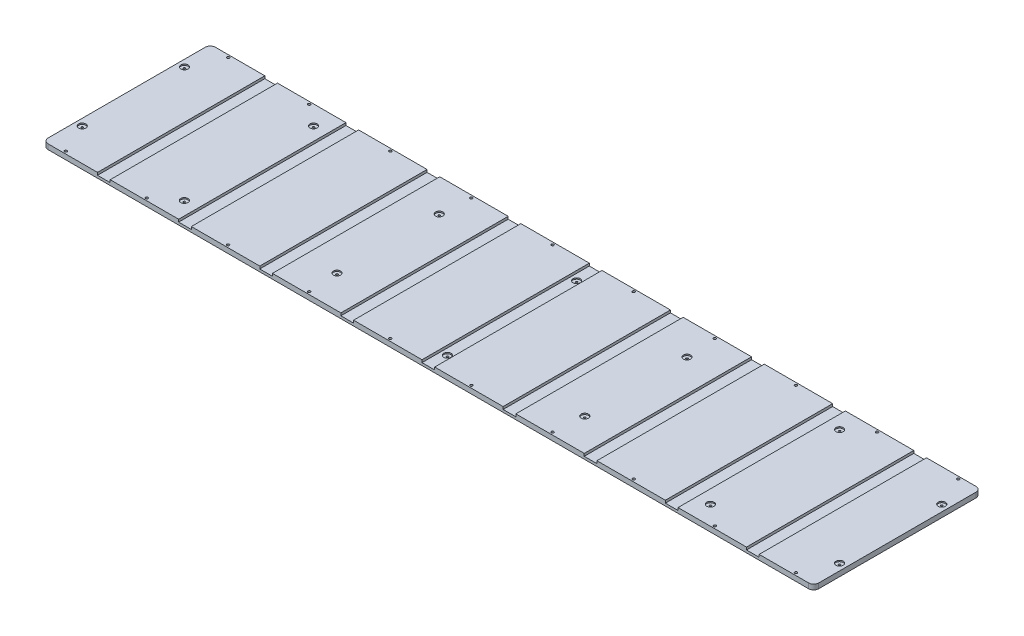
SolidWorks part; units mm, degrees
material "PE High Density"
ref_plane "Front Plane" through (0, 0, 0) normal (0, 0, 1) x (1, 0, 0)
ref_plane "Top Plane" through (0, 0, 0) normal (0, 1, 0) x (1, 0, 0)
ref_plane "Right Plane" through (0, 0, 0) normal (1, 0, 0) x (0, 0, -1)
sketch "Sketch1" plane through (0, 0, 0) normal (0, 1, 0) x (1, 0, 0)
  line L1 (0, 0) -> (1930.4, 0)
  line L2 (0, 0) -> (0, 419.1)
  line L3 (0, 419.1) -> (1930.4, 419.1)
  line L4 (1930.4, 0) -> (1930.4, 419.1)
  dimension "D1" = 1930.4
  dimension "D2" = 419.1
extrude "Boss-Extrude1" add sketch "Sketch1" along normal blind 12.7
sketch "Sketch2" plane through (0, 12.7, 0) normal (0, 1, 0) x (1, 0, 0)
  line L0 (1930.4, 419.1) -> (0, 419.1) construction
  line L2 (0, 419.1) -> (0, 0) construction
  line L3 (965.2, 419.1) -> (965.2, 0) construction
  line L4 (0, 0) -> (1930.4, 0) construction
  circle A0 centre (16.6688, 337.566) radius 2.4511
  circle A1 centre (654.8438, 337.566) radius 2.4511
  circle A2 centre (654.8438, 81.534) radius 2.4511
  circle A3 centre (16.6688, 81.534) radius 2.4511
  circle A4 centre (1275.5562, 337.566) radius 2.4511
  circle A5 centre (1275.5563, 81.534) radius 2.4511
  circle A6 centre (1913.7312, 337.566) radius 2.4511
  circle A7 centre (1913.7312, 81.534) radius 2.4511
  point P0 (16.6688, 337.566)
  point P5 (654.8438, 337.566)
  point P10 (654.8438, 81.534)
  point P17 (16.6688, 81.534)
  point P20 (1293.0187, 337.566)
  point P21 (1293.0187, 81.534)
  point P22 (1931.1937, 81.534)
  point P23 (1931.1937, 337.566)
  point P24 (1275.5562, 337.566)
  point P25 (1275.5563, 81.534)
  point P26 (1913.7312, 81.534)
  point P27 (1913.7312, 337.566)
  point P44 (0, 209.55)
  dimension "D7" = 4.9022
  dimension "D5" = 16.6687
  dimension "D6" = 256.032
  dimension "D4" = 638.175
  dimension "D1" = 128.016
  dimension "D2" = 4
  dimension "D3" = 2
sketch "Sketch7" plane through (0, 12.7, 0) normal (0, 1, 0) x (1, 0, 0)
  line L0 (0, 419.1) -> (0, 0) construction
  line L1 (0, 371.348) -> (1930.4, 371.348) construction
  line L2 (1930.4, 0) -> (1930.4, 419.1) construction
  circle A0 centre (306.324, 371.348) radius 2.4511
  circle A1 centre (306.324, 47.752) radius 2.4511
  circle A2 centre (965.2, 47.752) radius 2.4511
  circle A3 centre (965.2, 371.348) radius 2.4511
  circle A4 centre (1624.076, 371.348) radius 2.4511
  circle A5 centre (1624.076, 47.752) radius 2.4511
  point P0 (306.324, 371.348)
  point P3 (0, 209.55)
  point P8 (965.2, 371.348)
  point P9 (1624.076, 371.348)
  point P13 (965.2, 47.752)
  point P14 (1624.076, 47.752)
  point P18 (306.324, 47.752)
  dimension "D7" = 4.9022
  dimension "D5" = 658.876
  dimension "D6" = 323.596
  dimension "D2" = 161.798
  dimension "D3" = 3
  dimension "D4" = 2
fillet "Fillet1" radius 12.7 4 edges at (1930.4, 6.35, 0) (1930.4, 6.35, -419.1) (0, 6.35, 0) (0, 6.35, -419.1)
sketch "Sketch8" plane through (0, 12.7, 0) normal (0, 1, 0) x (1, 0, 0)
  line L0 (136.525, 419.1) -> (136.525, 0)
  line L1 (1917.7, 419.1) -> (12.7, 419.1) construction
  line L2 (12.7, 0) -> (1917.7, 0) construction
  line L3 (168.275, 419.1) -> (168.275, 0)
  line L4 (136.525, 419.1) -> (168.275, 419.1)
  line L5 (136.525, 0) -> (168.275, 0)
  line L6 (0, 406.4) -> (0, 12.7) construction
  line L7 (339.725, 0) -> (371.475, 0)
  line L8 (371.475, 419.1) -> (371.475, 0)
  line L9 (339.725, 419.1) -> (371.475, 419.1)
  line L10 (339.725, 419.1) -> (339.725, 0)
  line L11 (542.925, 0) -> (574.675, 0)
  line L12 (574.675, 419.1) -> (574.675, 0)
  line L13 (542.925, 419.1) -> (574.675, 419.1)
  line L14 (542.925, 419.1) -> (542.925, 0)
  line L15 (746.125, 0) -> (777.875, 0)
  line L16 (777.875, 419.1) -> (777.875, 0)
  line L17 (746.125, 419.1) -> (777.875, 419.1)
  line L18 (746.125, 419.1) -> (746.125, 0)
  line L19 (949.325, 0) -> (981.075, 0)
  line L20 (981.075, 419.1) -> (981.075, 0)
  line L21 (949.325, 419.1) -> (981.075, 419.1)
  line L22 (949.325, 419.1) -> (949.325, 0)
  line L23 (1152.525, 0) -> (1184.275, 0)
  line L24 (1184.275, 419.1) -> (1184.275, 0)
  line L25 (1152.525, 419.1) -> (1184.275, 419.1)
  line L26 (1152.525, 419.1) -> (1152.525, 0)
  line L27 (1355.725, 0) -> (1387.475, 0)
  line L28 (1387.475, 419.1) -> (1387.475, 0)
  line L29 (1355.725, 419.1) -> (1387.475, 419.1)
  line L30 (1355.725, 419.1) -> (1355.725, 0)
  line L31 (1558.925, 0) -> (1590.675, 0)
  line L32 (1590.675, 419.1) -> (1590.675, 0)
  line L33 (1558.925, 419.1) -> (1590.675, 419.1)
  line L34 (1558.925, 419.1) -> (1558.925, 0)
  line L35 (1762.125, 0) -> (1793.875, 0)
  line L36 (1793.875, 419.1) -> (1793.875, 0)
  line L37 (1762.125, 419.1) -> (1793.875, 419.1)
  line L38 (1762.125, 419.1) -> (1762.125, 0)
  dimension "D1" = 31.75
  dimension "D2" = 136.525
  dimension "D4" = 203.2
  dimension "D3" = 9
extrude "Cut-Extrude3" cut sketch "Sketch8" against normal blind 6.35
hole_wizard "1/4 (0.25) Diameter Hole1" positions "Sketch9" profile "Sketch10" hole size "1/4" standard "ANSI Inch" end condition through all
sketch "Sketch9" plane through (0, 12.7, 0) normal (0, 1, 0) x (1, 0, 0)
  line L1 (168.275, 0) -> (339.725, 0) construction
  line L2 (168.275, 0) -> (168.275, 419.1) construction
  line L3 (0, 209.55) -> (1930.4, 209.55) construction
  line L4 (0, 406.4) -> (0, 12.7) construction
  line L5 (1930.4, 12.7) -> (1930.4, 406.4) construction
  point P8 (254, 6.35)
  point P33 (457.2, 6.35)
  point P34 (660.4, 6.35)
  point P35 (863.6, 6.35)
  point P36 (1066.8, 6.35)
  point P37 (1270, 6.35)
  point P38 (1473.2, 6.35)
  point P39 (1676.4, 6.35)
  point P40 (254, 6.35)
  point P41 (457.2, 6.35)
  point P42 (660.4, 6.35)
  point P43 (863.6, 6.35)
  point P44 (1066.8, 6.35)
  point P45 (1270, 6.35)
  point P46 (1473.2, 6.35)
  point P47 (50.8, 6.35)
  point P48 (1879.6, 6.35)
  point P49 (1676.4, 6.35)
  point P50 (1676.4, 412.75)
  point P51 (1879.6, 412.75)
  point P52 (50.8, 412.75)
  point P53 (1473.2, 412.75)
  point P54 (1270, 412.75)
  point P55 (1066.8, 412.75)
  point P56 (863.6, 412.75)
  point P57 (660.4, 412.75)
  point P58 (457.2, 412.75)
  point P59 (254, 412.75)
  dimension "D1" = 6.35
  dimension "D2" = 85.725
  dimension "D5" = 203.2
  dimension "D3" = 9
  dimension "D4" = 2
sketch "Sketch10" plane through (254, 12.7, -6.35) normal (1, 0, 0) x (0, 0, 1)
  line L0 (0, 0) -> (0, 12.7)
  line L1 (0, 12.7) -> (3.175, 12.7)
  line L2 (3.175, 12.7) -> (3.175, 0)
  line L5 (3.175, 0) -> (0, 0)
  line L11 (0, -6.35) -> (0, 107.95) construction
  dimension "Thru Hole Dia." = 6.35
  dimension "Thru Hole Depth" = 12.7
hole_wizard "CBORE for #10 Socket Head Cap Screw1" positions "Sketch11" profile "Sketch12" counterbore size "#10" standard "ANSI Inch" end condition through all
sketch "Sketch11" plane through (0, 12.7, 0) normal (0, 1, 0) x (1, 0, 0)
  point P0 (16.6688, 337.566)
  point P3 (16.6688, 81.534)
  point P6 (306.324, 47.752)
  point P9 (306.324, 371.348)
  point P12 (654.8438, 337.566)
  point P15 (654.8438, 81.534)
  point P18 (965.2, 371.348)
  point P21 (965.2, 47.752)
  point P24 (1275.5563, 81.534)
  point P27 (1275.5562, 337.566)
  point P30 (1624.076, 371.348)
  point P33 (1624.076, 47.752)
  point P36 (1913.7312, 81.534)
  point P39 (1913.7312, 337.566)
sketch "Sketch12" plane through (16.6688, 12.7, -337.566) normal (1, 0, 0) x (0, 0, 1)
  line L0 (0, 0) -> (0, 12.7)
  line L1 (0, 12.7) -> (2.4511, 12.7)
  line L3 (2.4511, 12.7) -> (2.4511, 3.175)
  line L4 (2.4511, 3.175) -> (9.0488, 3.175)
  line L5 (9.0488, 3.175) -> (9.0488, 0)
  line L7 (9.0488, 0) -> (0, 0)
  line L11 (0, -6.35) -> (0, 107.95) construction
  dimension "Thru Hole Dia." = 4.9022
  dimension "Thru Hole Depth" = 12.7
  dimension "C'Bore Dia." = 18.0975
  dimension "C'Bore Depth" = 3.175
hole_wizard "CBORE for #10 Binding Head Machine Screw1" positions "Sketch13" profile "Sketch14" counterbore size "#10" standard "ANSI Inch" end condition through all
sketch "Sketch13" plane through (0, 6.35, 0) normal (0, 1, 0) x (1, 0, 0)
  circle A0 centre (965.2, 371.348) radius 2.4511 construction
  circle A1 centre (965.2, 47.752) radius 2.4511 construction
  point P0 (965.2, 371.348)
  point P3 (965.2, 47.752)
sketch "Sketch14" plane through (965.2, 6.35, -371.348) normal (1, 0, 0) x (0, 0, 1)
  line L0 (0, 0) -> (0, 6.35)
  line L1 (0, 6.35) -> (2.4511, 6.35)
  line L3 (2.4511, 6.35) -> (2.4511, 3.175)
  line L4 (2.4511, 3.175) -> (9.0488, 3.175)
  line L5 (9.0488, 3.175) -> (9.0488, 0)
  line L7 (9.0488, 0) -> (0, 0)
  line L11 (0, -6.35) -> (0, 107.95) construction
  dimension "Thru Hole Dia." = 4.9022
  dimension "Thru Hole Depth" = 6.35
  dimension "C'Bore Dia." = 18.0975
  dimension "C'Bore Depth" = 3.175
equation "\"D1@Sketch2\"=\"D6@Sketch2\"/2"
equation "\"D2@Sketch7\"=\"D6@Sketch7\"/2"
